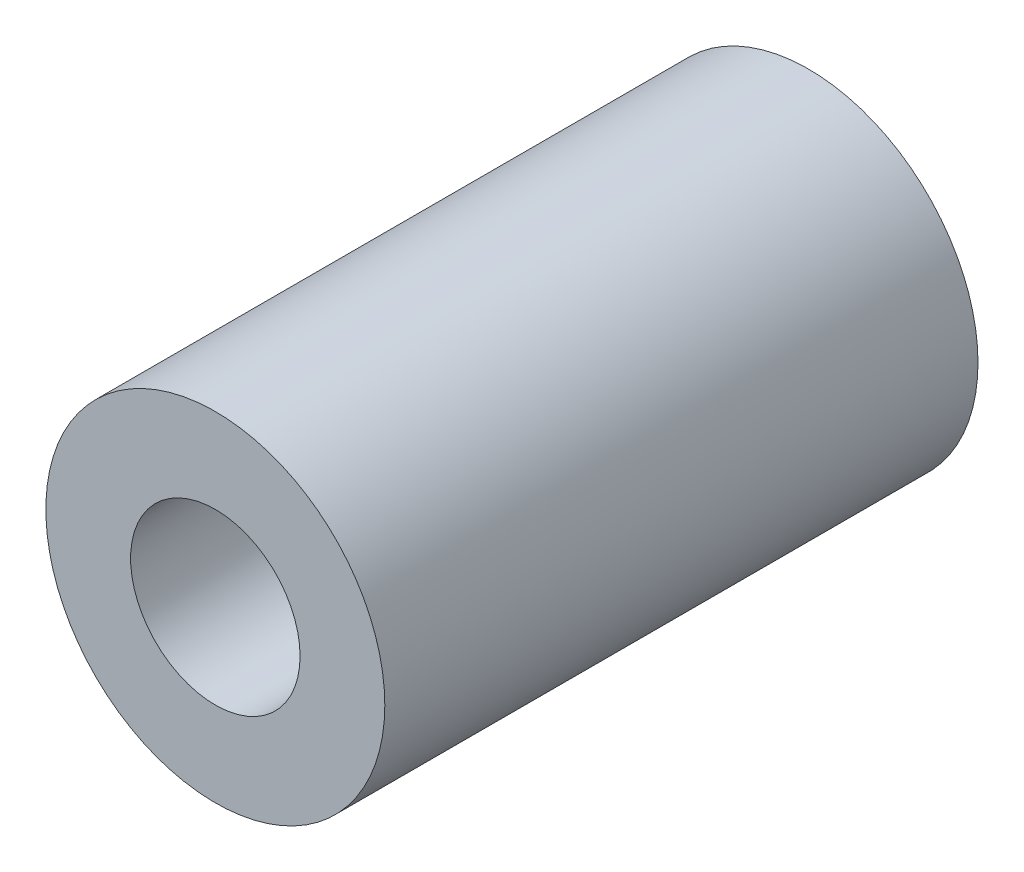
SolidWorks part; units mm, degrees
ref_plane "Plan de face" through (0, 0, 0) normal (0, 0, 1) x (1, 0, 0)
ref_plane "Plan de dessus" through (0, 0, 0) normal (0, 1, 0) x (1, 0, 0)
ref_plane "Plan de droite" through (0, 0, 0) normal (1, 0, 0) x (0, 0, -1)
sketch "Esquisse1" plane through (0, 0, 0) normal (0, 0, 1) x (1, 0, 0)
  circle A0 centre (0, 0) radius 10
  circle A1 centre (0, 0) radius 20
  dimension "D1" = 40
  dimension "D2" = 20
extrude "Boss.-Extru.1" add sketch "Esquisse1" along normal mid plane 70
